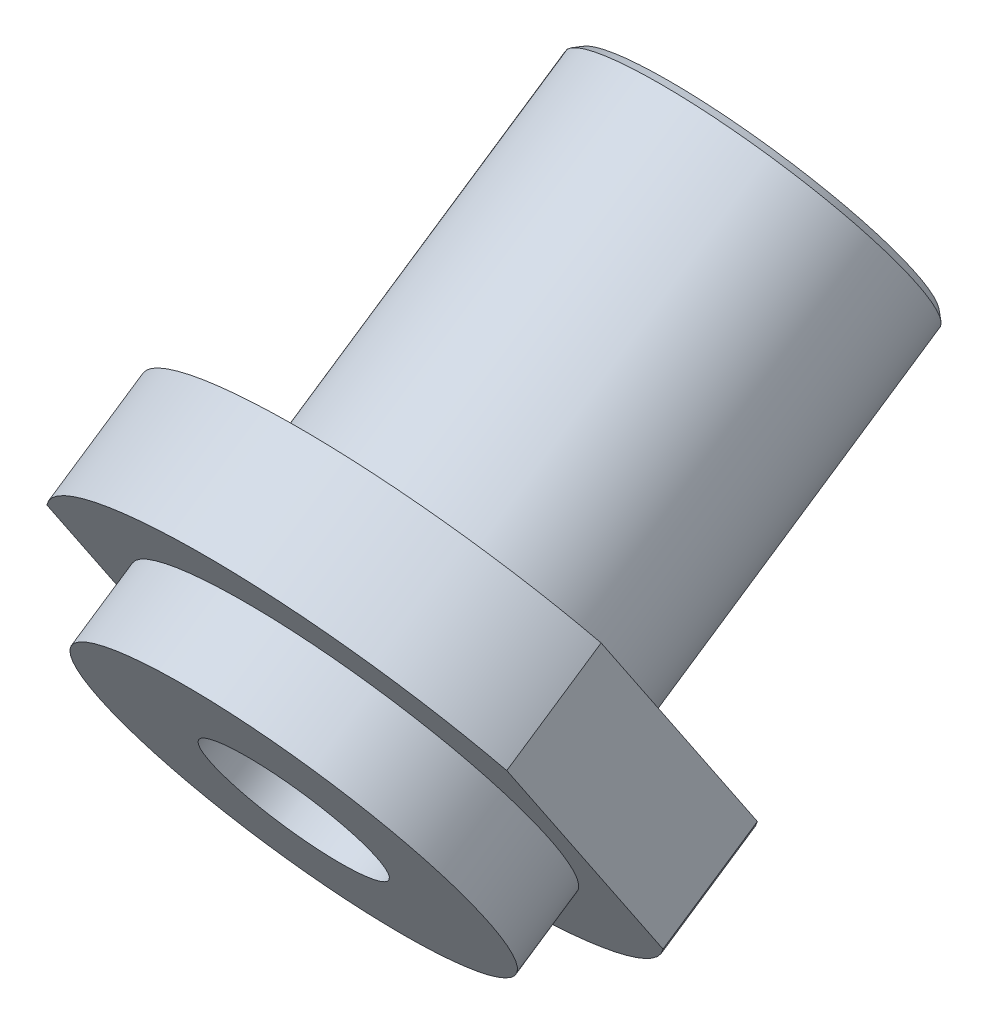
SolidWorks part; units mm, degrees
material "AISI 4130 Steel (McMaster EZ Weld Tubes)"
ref_plane "Front Plane" through (0, 0, 0) normal (0, 0, 1) x (1, 0, 0)
ref_plane "Top Plane" through (0, 0, 0) normal (0, 1, 0) x (1, 0, 0)
ref_plane "Right Plane" through (0, 0, 0) normal (1, 0, 0) x (0, 0, -1)
sketch "Sketch2" plane through (0, -87.3155, 130.0725) normal (0, -0.5574, 0.8303) x (1, 0, 0)
  circle A0 centre (0, 484.5115) radius 6.6929 construction
  circle A1 centre (0, 484.5115) radius 6.6929
extrude "Boss-Extrude1" add sketch "Sketch2" against normal blind 15.113
sketch "Sketch3" plane through (0, -87.3155, 130.0725) normal (0, -0.5574, 0.8303) x (1, 0, 0)
  line L4 (-9.3497, 478.812) -> (-9.3497, 490.2109)
  line L5 (9.3497, 478.812) -> (9.3497, 490.2109)
  arc A0 (9.3497, 490.2109) -> (-9.3497, 490.2109) centre (0, 484.5115) ccw
  arc A5 (-9.3497, 478.812) -> (9.3497, 478.812) centre (0, 484.5115) ccw
  arc A6 (9.3497, 490.2109) -> (-9.3497, 490.2109) centre (0, 484.5115) ccw
  circle M6 centre (0, 484.5115) radius 6.6929
  dimension "D1" = 10.9499
  dimension "D2" = 9.3497
extrude "Boss-Extrude2" add sketch "Sketch3" along normal blind 4.6203 contours L4 A5 L5 A0 M6 | M6
sketch "Sketch4" plane through (0, -89.8906, 133.9086) normal (0, -0.5574, 0.8303) x (1, 0, 0)
  circle A0 centre (0, 484.5115) radius 7.9502
  dimension "D1" = 15.9004
extrude "Boss-Extrude3" add sketch "Sketch4" along normal blind 2.9997
hole_wizard "M8x1.25 Tapped Hole1" positions "Sketch5" profile "Sketch6" tap size "M8x1.25" standard "ANSI Metric" end condition through all
sketch "Sketch5" plane through (0, -91.5625, 136.3992) normal (0, -0.5574, 0.8303) x (1, 0, 0)
  point P0 (0, 484.5115)
sketch "Sketch6" plane through (0, 310.7161, 406.4422) normal (1, 0, 0) x (0, -0.8303, -0.5574)
  line L0 (0, 0) -> (0, 28.9274)
  line L1 (0, 28.9274) -> (3.4, 28.9274)
  line L2 (3.4, 28.9274) -> (3.4, 0)
  line L5 (3.4, 0) -> (0, 0)
  line L11 (0, -6.35) -> (0, 107.95) construction
  dimension "Thru Tap Drill Dia." = 6.8
  dimension "Thru Tap Drill Depth" = 28.9274
cosmetic thread "Hole Thread1" parameters "D2"=8
chamfer "Chamfer2" distance 0.254 angle 45 1 edges at (0, 317.8294, 383.8372)
